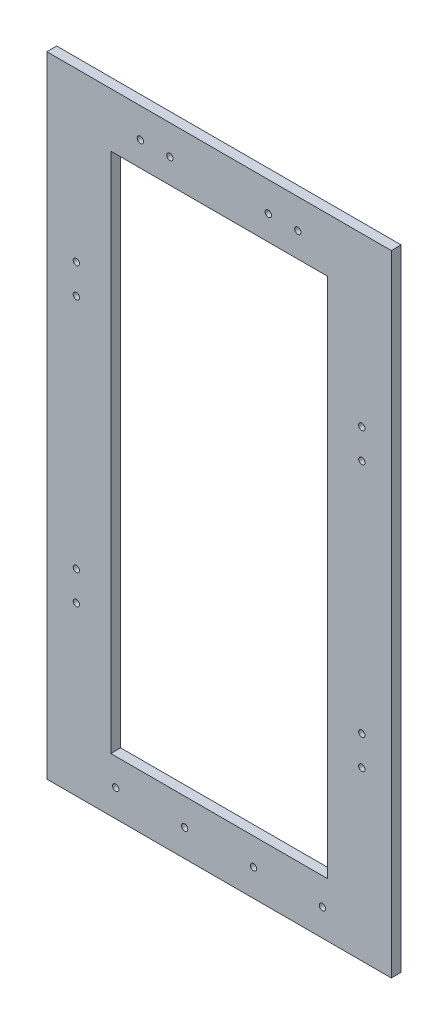
SolidWorks part; units mm, degrees
ref_plane "Front Plane" through (0, 0, 0) normal (0, 0, 1) x (1, 0, 0)
ref_plane "Top Plane" through (0, 0, 0) normal (0, 1, 0) x (1, 0, 0)
ref_plane "Right Plane" through (0, 0, 0) normal (1, 0, 0) x (0, 0, -1)
sketch "Sketch1" plane through (0, 0, 0) normal (0, 0, 1) x (1, 0, 0)
  line L1 (-87.5, -160) -> (87.5, -160)
  line L2 (-87.5, -160) -> (-87.5, 160)
  line L3 (-87.5, 160) -> (87.5, 160)
  line L4 (87.5, -160) -> (87.5, 160)
  line L5 (-87.5, -160) -> (87.5, 160) construction
  line L6 (-87.5, 160) -> (87.5, -160) construction
  point P0 (0, 0)
  dimension "D1" = 320
  dimension "D2" = 175
extrude "Boss-Extrude1" add sketch "Sketch1" along normal blind 5
sketch "Sketch2" plane through (0, 0, 0) normal (0, 0, -1) x (-1, 0, 0)
  line L1 (55, -132.5) -> (-55, -132.5)
  line L2 (55, -132.5) -> (55, 132.5)
  line L3 (55, 132.5) -> (-55, 132.5)
  line L4 (-55, -132.5) -> (-55, 132.5)
  line L5 (55, -132.5) -> (-55, 132.5) construction
  line L6 (55, 132.5) -> (-55, -132.5) construction
  point P0 (0, 0)
  dimension "D1" = 110
  dimension "D2" = 265
extrude "Cut-Extrude1" cut sketch "Sketch2" against normal up to next
sketch "Sketch4" plane through (0, 0, 0) normal (0, 0, -1) x (-1, 0, 0)
  line L0 (0, 160) -> (0, 145) construction
  line L2 (-87.5, 160) -> (87.5, 160) construction
  line L3 (0, 145) -> (-25, 145) construction
  line L4 (-25, 145) -> (-40, 145) construction
  circle A0 centre (-25, 145) radius 1.6
  circle A1 centre (-40, 145) radius 1.6
  circle A2 centre (25, 145) radius 1.6
  circle A3 centre (40, 145) radius 1.6
  dimension "D4" = 3.2
  dimension "D5" = 3.2
  dimension "D1" = 15
  dimension "D2" = 25
  dimension "D3" = 15
extrude "Cut-Extrude2" cut sketch "Sketch4" against normal up to next
sketch "Sketch5" plane through (0, 0, 0) normal (0, 0, -1) x (-1, 0, 0)
  line L0 (-87.5, 0) -> (-72.5, 0) construction
  line L1 (-87.5, -160) -> (-87.5, 160) construction
  line L2 (-72.5, 0) -> (-72.5, 60) construction
  line L3 (-72.5, 60) -> (-72.5, 75) construction
  line L5 (0, 0) -> (0, 19.1648) construction
  circle A0 centre (-72.5, 75) radius 1.6
  circle A1 centre (-72.5, 60) radius 1.6
  circle A2 centre (-72.5, -75) radius 1.6
  circle A3 centre (-72.5, -60) radius 1.6
  circle A4 centre (72.5, -75) radius 1.6
  circle A5 centre (72.5, -60) radius 1.6
  circle A6 centre (72.5, 60) radius 1.6
  circle A7 centre (72.5, 75) radius 1.6
  dimension "D2" = 3.2
  dimension "D3" = 3.2
  dimension "D1" = 15
  dimension "D4" = 15
  dimension "D5" = 60
extrude "Cut-Extrude3" cut sketch "Sketch5" against normal up to next
sketch "Sketch6" plane through (0, 0, 0) normal (0, 0, -1) x (-1, 0, 0)
  line L0 (0, -132.5) -> (0, -160) construction
  line L1 (-55, -132.5) -> (55, -132.5) construction
  line L2 (87.5, -160) -> (-87.5, -160) construction
  line L3 (87.5, -146.25) -> (52.5, -146.25) construction
  line L4 (87.5, 160) -> (87.5, -160) construction
  circle A0 centre (52.5, -146.25) radius 1.6
  circle A1 centre (17.5, -146.25) radius 1.6
  circle A2 centre (-17.5, -146.25) radius 1.6
  circle A3 centre (-52.5, -146.25) radius 1.6
  dimension "D2" = 3.2
  dimension "D1" = 35
  dimension "D3" = 4
extrude "Cut-Extrude4" cut sketch "Sketch6" against normal up to next and the other way through all
